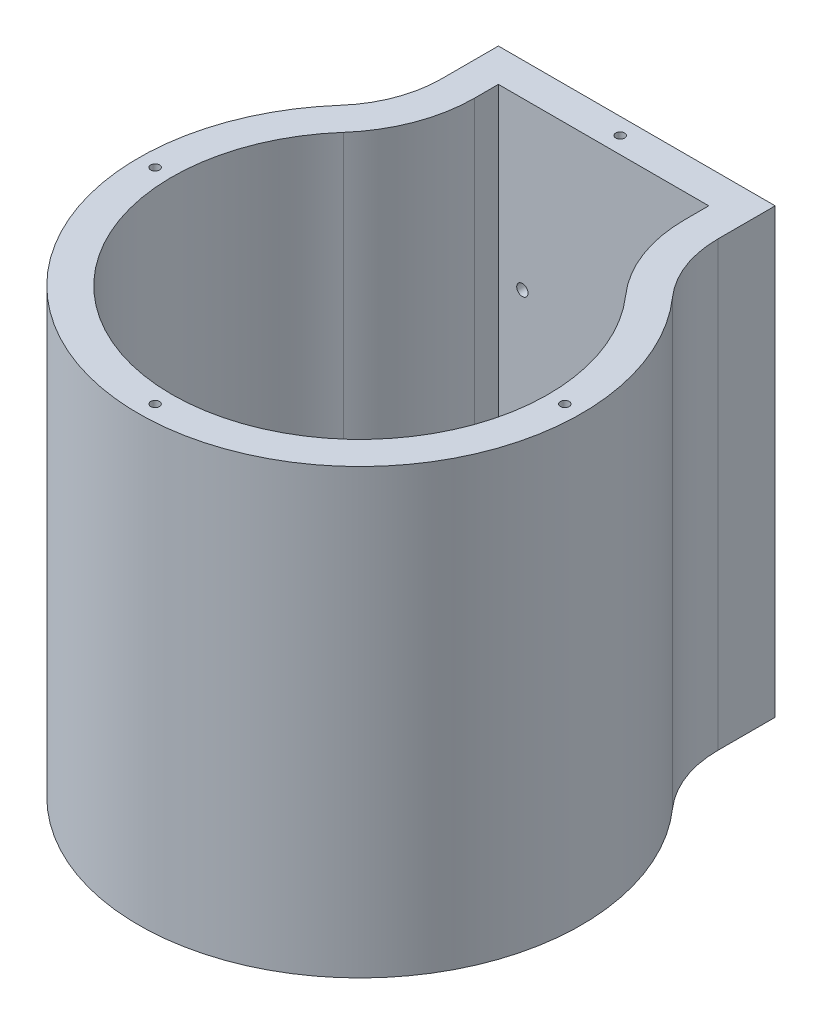
SolidWorks part; units mm, degrees
ref_plane "정면" through (0, 0, 0) normal (0, 0, 1) x (1, 0, 0)
ref_plane "윗면" through (0, 0, 0) normal (0, 1, 0) x (1, 0, 0)
ref_plane "우측면" through (0, 0, 0) normal (1, 0, 0) x (0, 0, -1)
ref_plane "평면1" through (0, 0, 0) normal (0, -1, 0) x (1, 0, 0)
sketch "스케치1" plane through (0, 0, 0) normal (0, -1, 0) x (1, 0, 0)
  line L0 (-25, -31.225) -> (-25, -50)
  line L1 (-25, -50) -> (25, -50)
  line L2 (25, -50) -> (25, -31.225)
  arc A0 (25, -31.225) -> (-25, -31.225) centre (0, 0) ccw
extrude "보스-돌출1" add sketch "스케치1" against normal blind 80
sketch "스케치2" plane through (0, 80, 0) normal (0, 1, 0) x (-1, 0, 0)
  line L0 (-19, -44) -> (19, -44)
  line L1 (19, -44) -> (19, -28.1957)
  line L2 (-19, -28.1957) -> (-19, -44)
  arc A0 (19, -28.1957) -> (-19, -28.1957) centre (0, 0) ccw
extrude "컷-돌출1" cut sketch "스케치2" against normal blind 74
hole_wizard "Ø2.05 (2.05) 지름 구멍1" positions "스케치4" profile "스케치3" hole size "Ø2.05" standard "Ansi Metric"
sketch "스케치4" plane through (0, 0, -50) normal (0, 0, -1) x (-1, 0, 0)
  point P0 (-14.6668, 50)
  point P1 (-14.6668, 30)
  point P2 (14.6668, 50)
  point P3 (14.6668, 30)
sketch "스케치3" plane through (14.6668, 50, -50) normal (1, 0, 0) x (0, 1, 0)
  line L0 (0, 0) -> (0, 6)
  line L1 (0, 6) -> (1.025, 6)
  line L2 (1.025, 6) -> (1.025, 0)
  line L5 (1.025, 0) -> (0, 0)
  line L11 (0, -6.35) -> (0, 107.95) construction
  dimension "관통 구멍 지름" = 2.05
  dimension "관통 구멍 깊이" = 6
hole_wizard "Ø1.6 (1.6) 지름 구멍1" positions "스케치6" profile "스케치5" hole size "Ø1.6" standard "Ansi Metric"
sketch "스케치6" plane through (0, 80, 0) normal (0, 1, 0) x (1, 0, 0)
  point P0 (0, 47)
  point P1 (-37, 0)
  point P2 (37, 0)
  point P3 (0, -37)
sketch "스케치5" plane through (0, 80, -47) normal (1, 0, 0) x (0, 0, 1)
  line L0 (0, 0) -> (0, 5.6807)
  line L1 (0, 5.6807) -> (0.8, 5.2)
  line L2 (0.8, 5.2) -> (0.8, 0)
  line L5 (0.8, 0) -> (0, 0)
  line L10 (0, 5.6807) -> (-0.8, 5.2) construction
  line L11 (0, -6.35) -> (0, 107.95) construction
  dimension "구멍 지름" = 1.6
  dimension "구멍 깊이" = 5.2
  dimension "드릴 각도" = 118
hole_wizard "M2 육각 머리 작은 나사용 카운터보어1" positions "스케치8" profile "스케치7" counterbore size "M2" standard "Ansi Metric"
sketch "스케치8" plane through (0, 6, 0) normal (0, 1, 0) x (1, 0, 0)
  point P0 (0, 8)
  point P1 (5.6569, 5.6569)
  point P2 (8, 0)
  point P3 (5.6569, -5.6569)
  point P4 (0, -8)
  point P5 (-5.6569, -5.6569)
  point P6 (-8, 0)
  point P7 (-5.6569, 5.6569)
sketch "스케치7" plane through (0, 6, -8) normal (1, 0, 0) x (0, 0, 1)
  line L0 (0, 0) -> (0, 6)
  line L1 (0, 6) -> (1.2, 6)
  line L3 (1.2, 6) -> (1.2, 2)
  line L4 (1.2, 2) -> (2.25, 2)
  line L5 (2.25, 2) -> (2.25, 0)
  line L7 (2.25, 0) -> (0, 0)
  line L11 (0, -6.35) -> (0, 107.95) construction
  dimension "관통 구멍 지름" = 2.4
  dimension "관통 구멍 깊이" = 6
  dimension "카운터보어 지름" = 4.5
  dimension "카운터보어 깊이" = 2
hole_wizard "구멍1" positions "스케치10" profile "스케치9" legacy
sketch "스케치10" plane through (0, 0, 0) normal (0, -1, 0) x (-1, 0, 0)
  point P0 (0, 0)
sketch "스케치9" plane through (0, 0, 0) normal (1, 0, 0) x (0, 0, -1)
  line L0 (0, 0) -> (0, 80)
  line L1 (0, 80) -> (2.5, 80)
  line L2 (2.5, 80) -> (2.5, 2.2)
  line L3 (2.5, 2.2) -> (5.5, 2.2)
  line L4 (5.5, 2.2) -> (5.5, 0)
  line L5 (5.5, 0) -> (0, 0)
  line L6 (0, 110) -> (0, -10) construction
  dimension "지름" = 5
  dimension "깊이" = 80
  dimension "카운터-보어 지름" = 11
  dimension "카운터-보어 깊이" = 2.2
fillet "필렛1" radius 20 2 edges at (-25, 40, -31.225) (25, 40, -31.225)
fillet "필렛2" radius 26 2 edges at (19, 43, -28.1957) (-19, 43, -28.1957)
